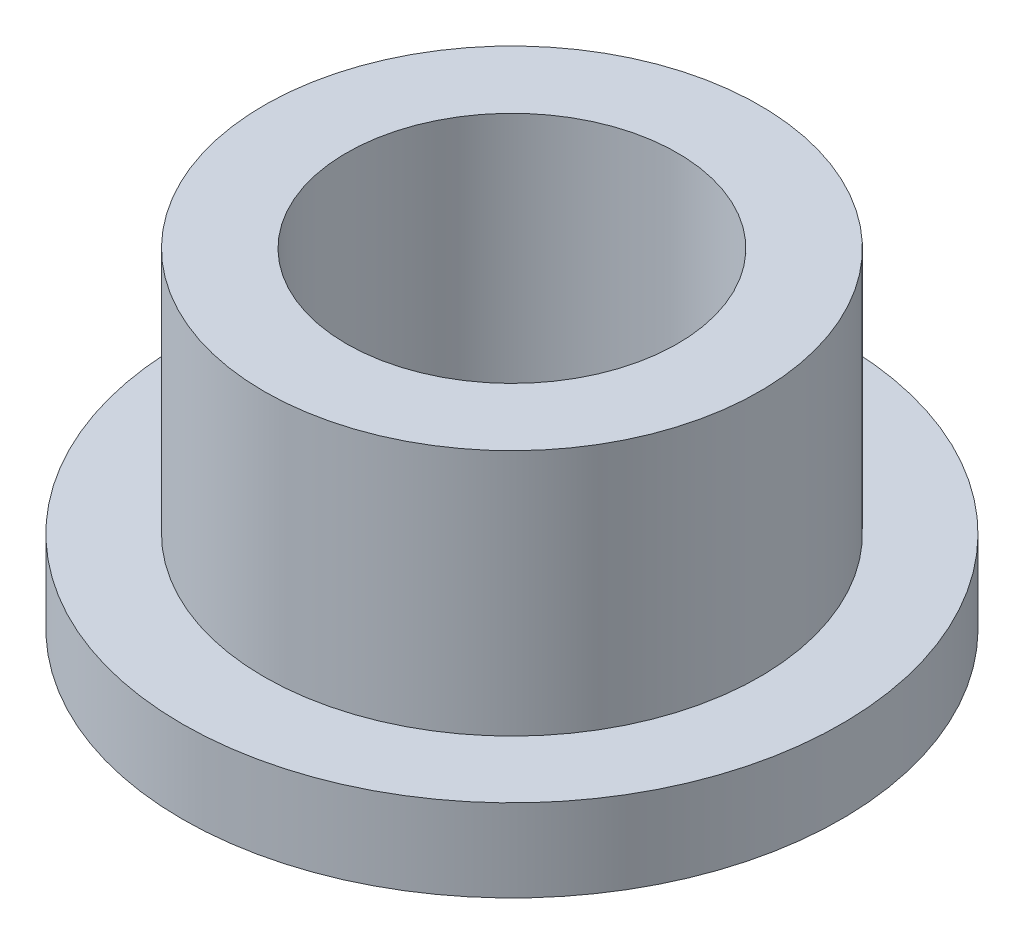
SolidWorks part; units mm, degrees
ref_plane "Front" through (0, 0, 0) normal (0, 0, 1) x (1, 0, 0)
ref_plane "Top" through (0, 0, 0) normal (0, 1, 0) x (1, 0, 0)
ref_plane "Right" through (0, 0, 0) normal (1, 0, 0) x (0, 0, -1)
sketch "Sketch1" plane through (0, 0, 0) normal (0, 1, 0) x (1, 0, 0)
  circle A0 centre (0, 0) radius 6.3754
  circle A1 centre (0, 0) radius 9.5504
  circle A2 centre (0, 0) radius 12.7
  dimension "ID" = 12.7508
  dimension "OD" = 19.1008
  dimension "FlangeOD" = 25.4
sketch "Sketch2" plane through (0, 0, 0) normal (0, 1, 0) x (1, 0, 0)
  circle A0 centre (0, 0) radius 6.3754 construction
  circle A1 centre (0, 0) radius 9.5504 construction
  circle A2 centre (0, 0) radius 6.3754
  circle A3 centre (0, 0) radius 9.5504
extrude "Boss-Extrude1" add sketch "Sketch2" along normal blind 12.7
sketch "Sketch3" plane through (0, 0, 0) normal (0, 1, 0) x (1, 0, 0)
  circle A0 centre (0, 0) radius 12.7 construction
  circle A1 centre (0, 0) radius 9.5504 construction
  circle A2 centre (0, 0) radius 12.7
  circle A3 centre (0, 0) radius 9.5504
extrude "Boss-Extrude2" add sketch "Sketch3" along normal blind 3.175
